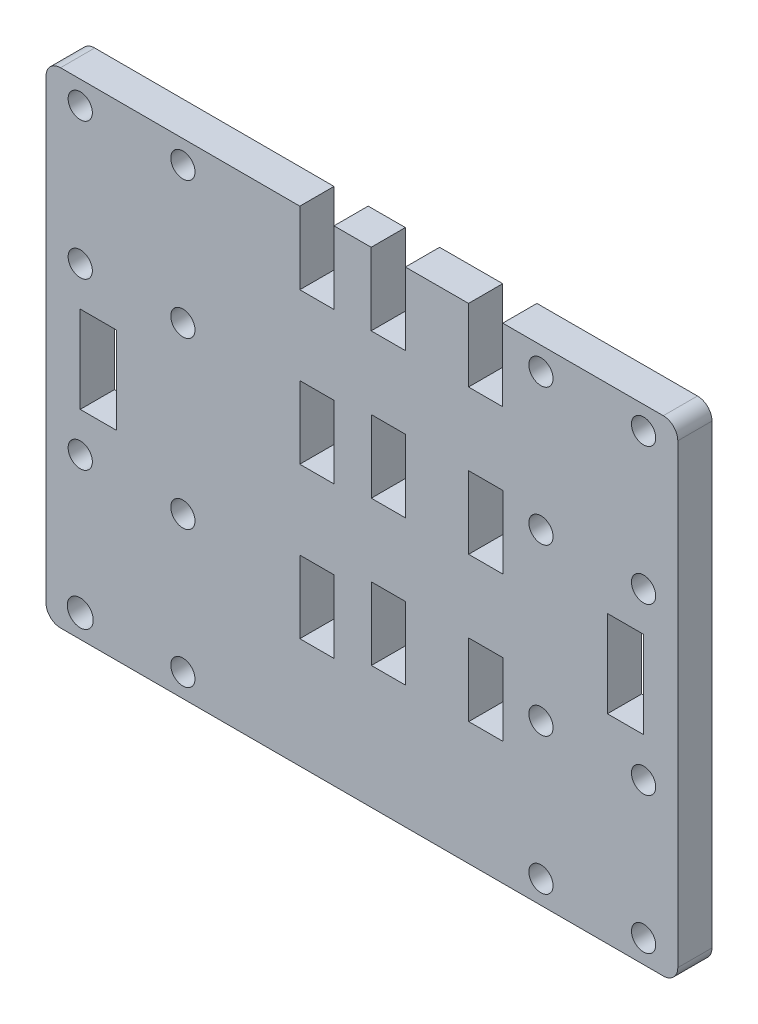
SolidWorks part; units mm, degrees
ref_plane "Front Plane" through (0, 0, 0) normal (0, 0, 1) x (1, 0, 0)
ref_plane "Top Plane" through (0, 0, 0) normal (0, 1, 0) x (1, 0, 0)
ref_plane "Right Plane" through (0, 0, 0) normal (1, 0, 0) x (0, 0, -1)
sketch "Sketch1" plane through (0, 0, 0) normal (0, 0, 1) x (1, 0, 0)
  line L0 (333.6594, 144.0694) -> (339.6538, 144.0694)
  line L1 (375.975, 144.0694) -> (270.255, 144.0694)
  line L2 (378.515, 146.6094) -> (378.515, 226.6327)
  line L3 (270.2574, 229.1713) -> (312.2247, 229.1314)
  line L4 (267.715, 146.6094) -> (267.715, 226.6313)
  line L5 (318.2191, 229.1365) -> (324.7384, 229.1406)
  line L6 (347.8135, 229.1551) -> (375.9734, 229.1727)
  line L7 (330.7408, 229.1406) -> (341.8152, 229.1551)
  line L8 (324.7384, 229.1406) -> (324.7384, 216.4444)
  line L9 (324.7384, 216.4444) -> (330.7408, 216.4444)
  line L10 (330.7408, 229.1406) -> (330.7408, 216.4444)
  line L11 (330.7487, 203.7444) -> (324.7623, 203.7444)
  line L12 (330.7487, 203.7444) -> (330.7487, 191.0406)
  line L13 (330.7487, 191.0406) -> (324.7623, 191.0406)
  line L14 (324.7623, 203.7444) -> (324.7623, 191.0406)
  line L15 (330.7646, 178.3444) -> (324.7782, 178.3444)
  line L16 (330.7646, 178.3444) -> (330.7646, 165.6406)
  line L17 (330.7646, 165.6406) -> (324.7782, 165.6406)
  line L19 (312.2247, 216.4314) -> (318.2191, 216.4314)
  line L20 (312.2247, 216.4314) -> (312.2247, 229.1365)
  line L21 (312.2247, 229.1365) -> (318.2191, 229.1365)
  line L22 (318.2191, 216.4314) -> (318.2191, 229.1365)
  line L23 (312.2247, 202.6314) -> (318.2191, 202.6314)
  line L24 (312.2247, 202.6314) -> (312.2247, 189.9314)
  line L25 (312.2247, 189.9314) -> (318.2191, 189.9314)
  line L26 (318.2191, 202.6314) -> (318.2191, 189.9314)
  line L27 (312.2247, 176.1314) -> (318.2191, 176.1314)
  line L28 (324.7782, 178.3444) -> (324.7782, 165.6406)
  line L29 (312.2247, 176.1314) -> (312.2247, 163.4314)
  line L30 (341.847, 165.6513) -> (347.8334, 165.6513)
  line L31 (341.847, 165.6513) -> (341.847, 178.3551)
  line L32 (341.847, 178.3551) -> (347.8334, 178.3551)
  line L33 (347.8334, 165.6513) -> (347.8334, 178.3551)
  line L34 (341.8311, 191.0513) -> (347.8175, 191.0513)
  line L35 (273.7094, 186.6203) -> (273.7094, 194.2403)
  line L36 (273.7094, 194.2403) -> (280.0594, 194.2403)
  line L37 (280.0594, 194.2403) -> (280.0594, 179.0003)
  line L38 (280.0594, 179.0003) -> (273.7094, 179.0003)
  line L39 (273.7094, 179.0003) -> (273.7094, 186.6203)
  line L40 (372.5206, 179.0003) -> (372.5206, 186.6203)
  line L41 (366.1706, 179.0003) -> (372.5206, 179.0003)
  line L42 (366.1706, 194.2403) -> (366.1706, 179.0003)
  line L43 (372.5206, 194.2403) -> (366.1706, 194.2403)
  line L44 (372.5206, 186.6203) -> (372.5206, 194.2403)
  line L45 (341.8311, 191.0513) -> (341.8311, 203.7551)
  line L46 (341.8311, 203.7551) -> (347.8175, 203.7551)
  line L47 (347.8175, 191.0513) -> (347.8175, 203.7551)
  line L48 (341.8152, 216.4513) -> (347.8135, 216.4513)
  line L49 (341.8152, 216.4513) -> (341.8152, 229.1551)
  line L50 (341.8152, 229.1551) -> (341.8152, 216.4513)
  line L51 (347.8135, 216.4513) -> (347.8135, 229.1551)
  line L52 (312.2247, 163.4314) -> (318.2191, 163.4314)
  line L53 (341.8311, 203.7551) -> (347.8175, 203.7551)
  line L54 (341.8311, 203.7551) -> (341.8311, 191.0513)
  line L55 (341.8311, 191.0513) -> (347.8175, 191.0513)
  line L56 (347.8175, 203.7551) -> (347.8175, 191.0513)
  line L57 (341.847, 178.3551) -> (347.8334, 178.3551)
  line L58 (341.847, 178.3551) -> (341.847, 165.6513)
  line L59 (341.847, 165.6513) -> (347.8334, 165.6513)
  line L60 (347.8334, 178.3551) -> (347.8334, 165.6513)
  line L61 (324.7782, 178.3444) -> (330.7646, 178.3444)
  line L62 (324.7782, 178.3444) -> (324.7782, 165.6406)
  line L63 (324.7782, 165.6406) -> (330.7646, 165.6406)
  line L64 (330.7646, 178.3444) -> (330.7646, 165.6406)
  line L65 (324.7623, 191.0406) -> (330.7487, 191.0406)
  line L66 (324.7623, 191.0406) -> (324.7623, 203.7444)
  line L67 (324.7623, 203.7444) -> (330.7487, 203.7444)
  line L68 (330.7487, 191.0406) -> (330.7487, 203.7444)
  line L69 (324.7384, 216.4444) -> (330.7408, 216.4444)
  line L70 (324.7384, 216.4444) -> (324.7384, 229.1406)
  line L71 (318.2191, 176.1314) -> (318.2191, 163.4314)
  line L72 (330.7408, 216.4444) -> (330.7408, 229.1406)
  line L74 (341.8152, 229.1551) -> (341.8152, 216.4513)
  line L75 (341.8152, 216.4513) -> (347.8135, 216.4513)
  line L76 (347.8135, 229.1551) -> (347.8135, 216.4513)
  circle A0 centre (372.515, 148.1123) radius 2.125
  circle A1 centre (354.515, 148.1123) radius 2.125
  circle A2 centre (372.515, 172.1123) radius 2.125
  circle A3 centre (354.515, 172.1123) radius 2.125
  circle A4 centre (291.715, 148.1123) radius 2.125
  circle A5 centre (273.715, 148.1123) radius 2.2816
  circle A6 centre (291.715, 172.1123) radius 2.125
  circle A7 centre (273.715, 172.1123) radius 2.125
  circle A8 centre (372.515, 201.1314) radius 2.125
  circle A9 centre (354.515, 201.1314) radius 2.125
  circle A10 centre (372.515, 225.1314) radius 2.125
  circle A11 centre (354.515, 225.1314) radius 2.125
  circle A12 centre (291.715, 201.1314) radius 2.125
  circle A13 centre (273.715, 201.1314) radius 2.125
  circle A14 centre (291.715, 225.1314) radius 2.125
  circle A15 centre (273.715, 225.1314) radius 2.125
  arc A16 (378.515, 226.6327) -> (375.9734, 229.1727) centre (375.975, 226.6327) ccw
  arc A17 (270.2574, 229.1713) -> (267.715, 226.6313) centre (270.255, 226.6313) ccw
  arc A18 (270.255, 144.0694) -> (267.715, 146.6094) centre (270.255, 146.6094) cw
  arc A19 (375.975, 144.0694) -> (378.515, 146.6094) centre (375.975, 146.6094) ccw
  dimension "D1" = 2.54
  dimension "D2" = 2.54
  dimension "D3" = 2.54
  dimension "D4" = 2.54
extrude "Boss-Extrude1" add sketch "Sketch1" along normal blind 5.9944
